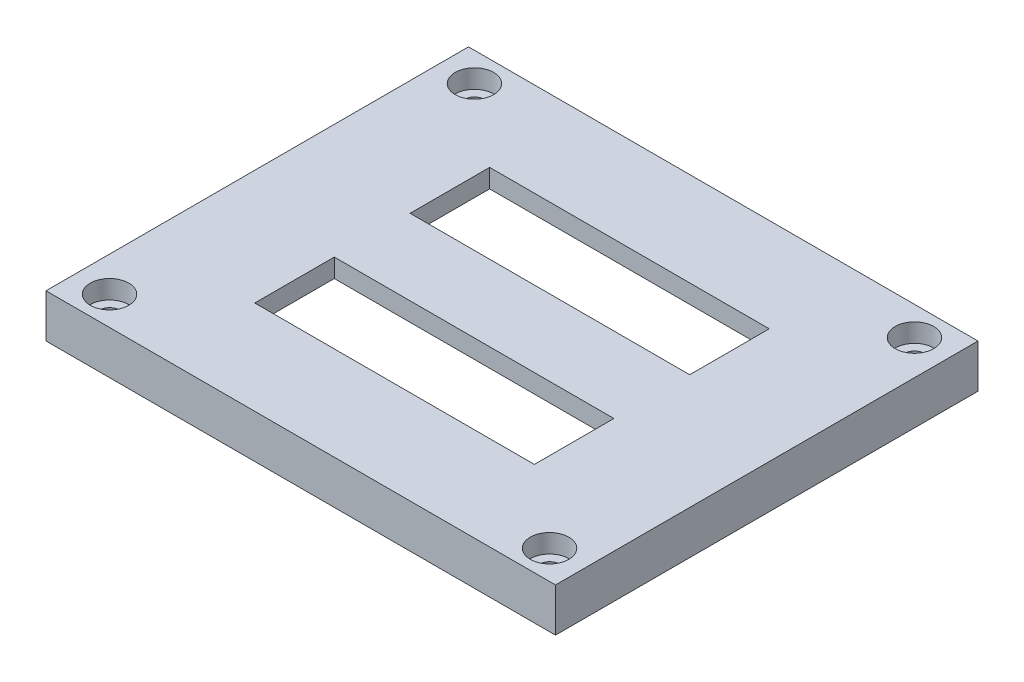
SolidWorks part; units mm, degrees
ref_plane "Спереди" through (0, 0, 0) normal (0, 0, 1) x (1, 0, 0)
ref_plane "Сверху" through (0, 0, 0) normal (0, 1, 0) x (1, 0, 0)
ref_plane "Справа" through (0, 0, 0) normal (1, 0, 0) x (0, 0, -1)
sketch "Sketch1" plane through (0, 0, 0) normal (0, 1, 0) x (1, 0, 0)
  line L1 (38, -31) -> (-38, -31)
  line L2 (38, -31) -> (38, 31)
  line L3 (38, 31) -> (-38, 31)
  line L4 (-38, -31) -> (-38, 31)
  line L5 (38, -31) -> (-38, 31) construction
  line L6 (38, 31) -> (-38, -31) construction
  point P0 (0, 0)
  dimension "D1" = 76
  dimension "D2" = 62
extrude "Boss-Extrude1" add sketch "Sketch1" along normal blind 2
sketch "Sketch2" plane through (0, 2, 0) normal (0, 1, 0) x (1, 0, 0)
  line L1 (-41, 34) -> (41, 34)
  line L2 (-41, 34) -> (-41, -34)
  line L3 (-41, -34) -> (41, -34)
  line L4 (41, 34) -> (41, -34)
  line L5 (-41, 34) -> (41, -34) construction
  line L6 (-41, -34) -> (41, 34) construction
  point P0 (0, 0)
  dimension "D1" = 82
  dimension "D2" = 68
extrude "Boss-Extrude2" add sketch "Sketch2" along normal blind 8
sketch "Sketch3" plane through (0, 0, 0) normal (0, -1, 0) x (1, 0, 0)
  line L0 (38, 0) -> (-38, 0) construction
  line L1 (0, -31) -> (0, 31) construction
  line L2 (38, -31) -> (-38, -31) construction
  line L3 (38, 31) -> (38, -31) construction
  line L4 (-38, -31) -> (-38, 31) construction
  line L5 (-38, 31) -> (38, 31) construction
  line L7 (-22.5, -18.9) -> (22.5, -18.9)
  line L8 (-22.5, -18.9) -> (-22.5, -6.1)
  line L9 (-22.5, 18.9) -> (22.5, 18.9)
  line L10 (-22.5, 18.9) -> (-22.5, 6.1)
  line L11 (-22.5, 6.1) -> (22.5, 6.1)
  line L12 (22.5, 18.9) -> (22.5, 6.1)
  line L13 (-22.5, 18.9) -> (22.5, 6.1) construction
  line L14 (-22.5, 6.1) -> (22.5, 18.9) construction
  line L15 (-22.5, -6.1) -> (22.5, -6.1)
  line L16 (22.5, -18.9) -> (22.5, -6.1)
  line L17 (-22.5, -18.9) -> (22.5, -6.1) construction
  line L18 (-22.5, -6.1) -> (22.5, -18.9) construction
  point P6 (0, 12.5)
  point P9 (0, -12.5)
  dimension "D1" = 45
  dimension "D2" = 12.8
  dimension "D3" = 25
  dimension "D4" = 12.5
extrude "Cut-Extrude1" cut sketch "Sketch3" against normal through all
sketch "Sketch4" plane through (0, 10, 0) normal (0, 1, 0) x (1, 0, 0)
  line L0 (41, 34) -> (-41, -34) construction
  line L1 (-41, 34) -> (41, -34) construction
  line L2 (-35.4089, 29.3635) -> (35.4089, 29.3635) construction
  line L3 (35.4089, 29.3635) -> (35.4089, -29.3635) construction
  line L4 (35.4089, -29.3635) -> (-35.4089, -29.3635) construction
  line L5 (-35.4089, -29.3635) -> (-35.4089, 29.3635) construction
  line L7 (-35.4089, -29.3635) -> (35.4089, 29.3635) construction
  line L8 (-35.4089, 29.3635) -> (35.4089, -29.3635) construction
  circle A0 centre (-35.4089, 29.3635) radius 1.6
  circle A1 centre (35.4089, 29.3635) radius 1.6
  circle A2 centre (35.4089, -29.3635) radius 1.6
  circle A3 centre (-35.4089, -29.3635) radius 1.6
  point P8 (0, 0)
  dimension "D2" = 3.2
  dimension "D1" = 92
extrude "Cut-Extrude2" cut sketch "Sketch4" against normal through all
sketch "Sketch5" plane through (0, 10, 0) normal (0, 1, 0) x (1, 0, 0)
  circle A0 centre (-35.4089, 29.3635) radius 3.1
  circle A1 centre (35.4089, 29.3635) radius 3.1
  circle A2 centre (35.4089, -29.3635) radius 3.1
  circle A3 centre (-35.4089, -29.3635) radius 3.1
  dimension "D1" = 6.2
extrude "Cut-Extrude3" cut sketch "Sketch5" against normal blind 3
sketch "Sketch9" plane through (0, 0, 0) normal (0, -1, 0) x (1, 0, 0)
  line L0 (-38, 31) -> (38, 31) construction
  line L1 (37.8, -30.8) -> (-37.8, -30.8)
  line L2 (37.8, -30.8) -> (37.8, 30.8)
  line L3 (37.8, 30.8) -> (-37.8, 30.8)
  line L4 (-37.8, -30.8) -> (-37.8, 30.8)
  line L5 (37.8, -30.8) -> (-37.8, 30.8) construction
  line L6 (37.8, 30.8) -> (-37.8, -30.8) construction
  line L7 (-38, -31) -> (-38, 31) construction
  point P0 (0, 0)
  dimension "D1" = 0.2
  dimension "D2" = 0.2
extrude "Cut-Extrude5" cut sketch "Sketch9" against normal blind 3 flip side to cut
sketch "Sketch10" plane through (0, 0, 0) normal (0, -1, 0) x (1, 0, 0)
  line L0 (-37.8, -30.8) -> (-31.8, -30.8)
  line L1 (-37.8, 24.8) -> (-37.8, 30.8)
  line L2 (34.7044, -30.8) -> (-34.7044, -30.8) construction
  line L3 (-37.8, 30.8) -> (-31.8, 30.8)
  line L4 (-31.8, -30.8) -> (-37.8, -24.8)
  line L5 (-37.8, 30.8) -> (-37.8, -30.8) construction
  line L6 (-37.8, -24.8) -> (-37.8, -30.8)
  line L7 (-34.7044, 30.8) -> (34.7044, 30.8) construction
  line L8 (-31.8, 30.8) -> (-37.8, 24.8)
  line L9 (37.8, 30.8) -> (37.8, 24.8)
  line L10 (37.8, -30.8) -> (37.8, 30.8) construction
  line L11 (37.8, 24.8) -> (31.8, 30.8)
  line L12 (31.8, 30.8) -> (37.8, 30.8)
  line L13 (37.8, -30.8) -> (31.8, -30.8)
  line L14 (31.8, -30.8) -> (37.8, -24.8)
  line L15 (37.8, -24.8) -> (37.8, -30.8)
  dimension "D1" = 6
extrude "Cut-Extrude6" cut sketch "Sketch10" against normal blind 3
sketch "Sketch11" plane through (0, 0, 0) normal (0, -1, 0) x (1, 0, 0)
  line L1 (-33, -27) -> (33, -27)
  line L2 (-33, -27) -> (-33, 27)
  line L3 (-33, 27) -> (33, 27)
  line L4 (33, -27) -> (33, 27)
  line L5 (-33, -27) -> (33, 27) construction
  line L6 (-33, 27) -> (33, -27) construction
  point P0 (0, 0)
  dimension "D1" = 54
  dimension "D2" = 66
extrude "Cut-Extrude7" cut sketch "Sketch11" against normal blind 7
chamfer "Chamfer2" distance 2 angle 10 2 edges at (-37.8, 0, 0) (37.8, 0, 0)
chamfer "Chamfer3" distance 1 angle 60 2 edges at (0, 0, 30.8) (0, 0, -30.8)
